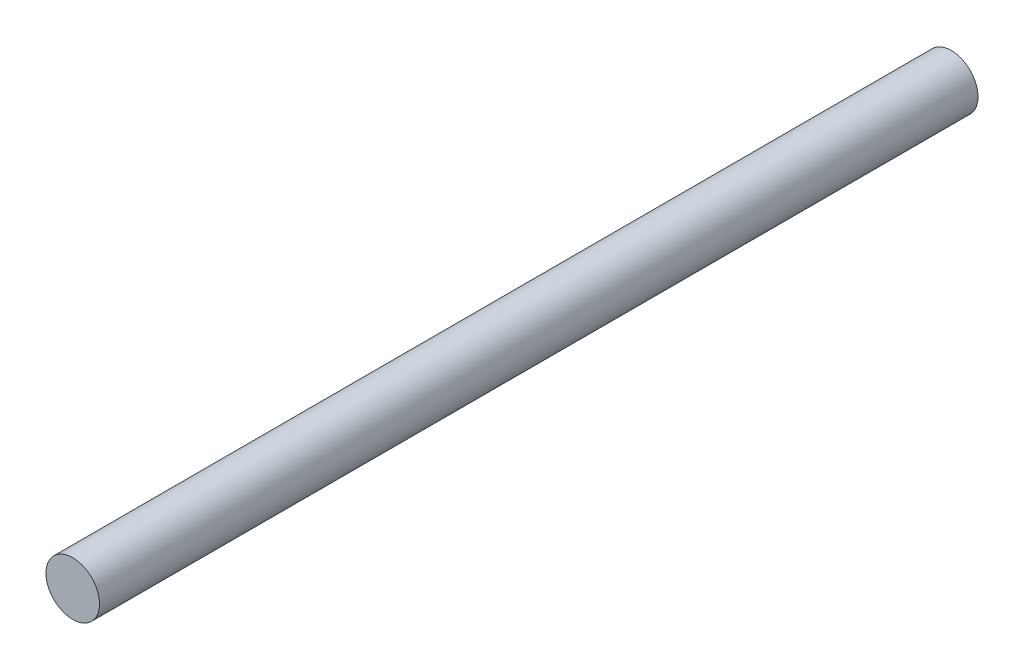
SolidWorks part; units mm, degrees
ref_plane "Front Plane" through (0, 0, 0) normal (0, 0, 1) x (1, 0, 0)
ref_plane "Top Plane" through (0, 0, 0) normal (0, 1, 0) x (1, 0, 0)
ref_plane "Right Plane" through (0, 0, 0) normal (1, 0, 0) x (0, 0, -1)
sketch "Sketch1" plane through (0, 0, 0) normal (0, 0, 1) x (1, 0, 0)
  circle A0 centre (0, 0) radius 1.5875
  dimension "D1" = 3.175
extrude "Boss-Extrude1" add sketch "Sketch1" along normal blind 52.1
